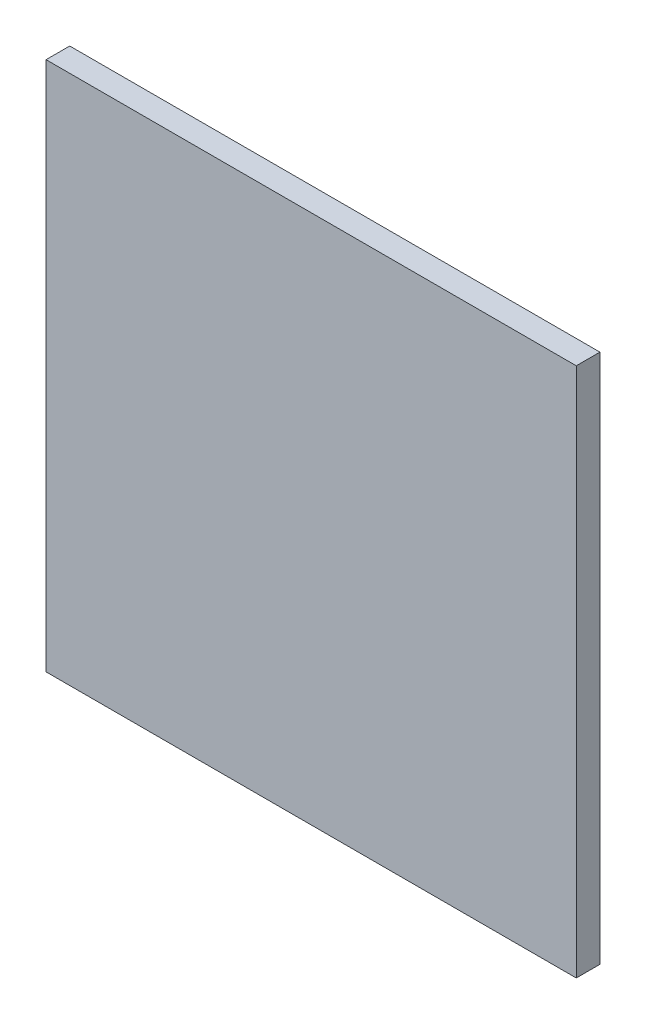
SolidWorks part; units mm, degrees
ref_plane "Front Plane" through (0, 0, 0) normal (0, 0, 1) x (1, 0, 0)
ref_plane "Top Plane" through (0, 0, 0) normal (0, 1, 0) x (1, 0, 0)
ref_plane "Right Plane" through (0, 0, 0) normal (1, 0, 0) x (0, 0, -1)
sketch "Sketch1" plane through (0, 0, 0) normal (0, 0, 1) x (1, 0, 0)
  line L1 (-86.3941, 43.0777) -> (-15.2741, 43.0777)
  line L2 (-86.3941, 43.0777) -> (-86.3941, -28.0423)
  line L3 (-86.3941, -28.0423) -> (-15.2741, -28.0423)
  line L4 (-15.2741, 43.0777) -> (-15.2741, -28.0423)
  dimension "D1" = 71.12
  dimension "D2" = 71.12
extrude "Boss-Extrude1" add sketch "Sketch1" along normal blind 3.175 contours L1 L4 L3 L2
